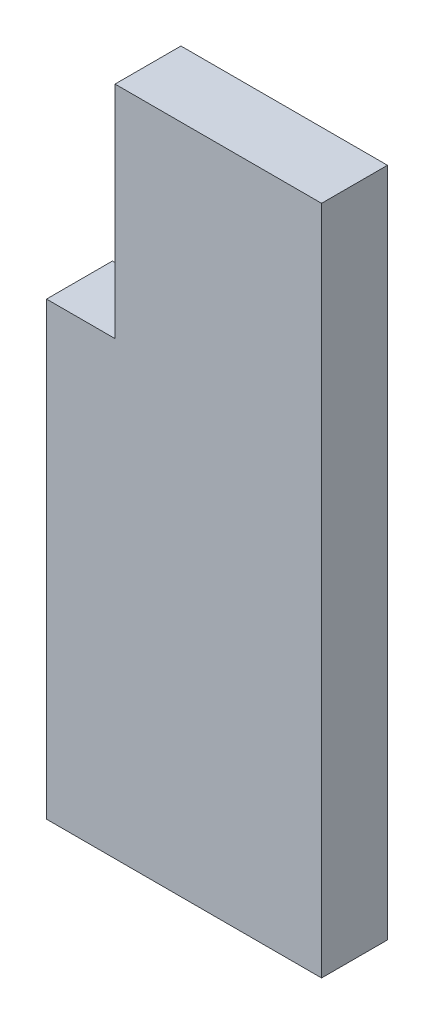
SolidWorks part; units mm, degrees
material "Acrylic (Medium-high impact)"
ref_plane "Front Plane" through (0, 0, 0) normal (0, 0, 1) x (1, 0, 0)
ref_plane "Top Plane" through (0, 0, 0) normal (0, 1, 0) x (1, 0, 0)
ref_plane "Right Plane" through (0, 0, 0) normal (1, 0, 0) x (0, 0, -1)
sketch "Sketch1" plane through (0, 0, 0) normal (0, 0, 1) x (1, 0, 0)
  line L0 (0, 0) -> (56.6, 0)
  line L1 (56.6, 0) -> (56.6, 21.7)
  line L2 (56.6, 21.7) -> (53.3, 21.7)
  line L3 (53.3, 21.7) -> (53.3, 32.32)
  line L4 (53.3, 32.32) -> (3.3, 32.32)
  line L5 (3.3, 32.32) -> (3.3, 21.7)
  line L6 (3.3, 21.7) -> (0, 21.7)
  line L7 (0, 21.7) -> (0, 0)
  line L8 (13.25, 15.66) -> (43.35, 15.66)
  line L9 (43.35, 15.66) -> (43.35, 32.32)
  line L10 (43.35, 32.32) -> (13.25, 32.32)
  line L11 (13.25, 32.32) -> (13.25, 15.66)
  point P13 (28.3, 15.66)
  point P14 (28.3, 0)
  dimension "D2" = 21.7
  dimension "D1" = 50
  dimension "D3" = 3.3
  dimension "D4" = 32.32
  dimension "D5" = 30.1
  dimension "D6" = 16.66
extrude "Boss-Extrude1" add sketch "Sketch1" along normal blind 3.175 contours L11 L4 L5 L6 L7 L0 L1 L2 L3 L9 L8
sketch "Sketch2" plane through (0, 0, 3.175) normal (0, 0, 1) x (1, 0, 0)
  line L0 (13.25, 32.32) -> (56.6, 32.32)
  line L1 (56.6, 32.32) -> (56.6, 0)
  line L2 (56.6, 0) -> (13.25, 0)
  line L3 (0, 0) -> (56.6, 0) construction
  line L4 (13.25, 0) -> (13.25, 32.32)
extrude "Cut-Extrude1" cut sketch "Sketch2" against normal up to surface (3.175 mm away) up to face at (28.3, 20.6167, 0)
